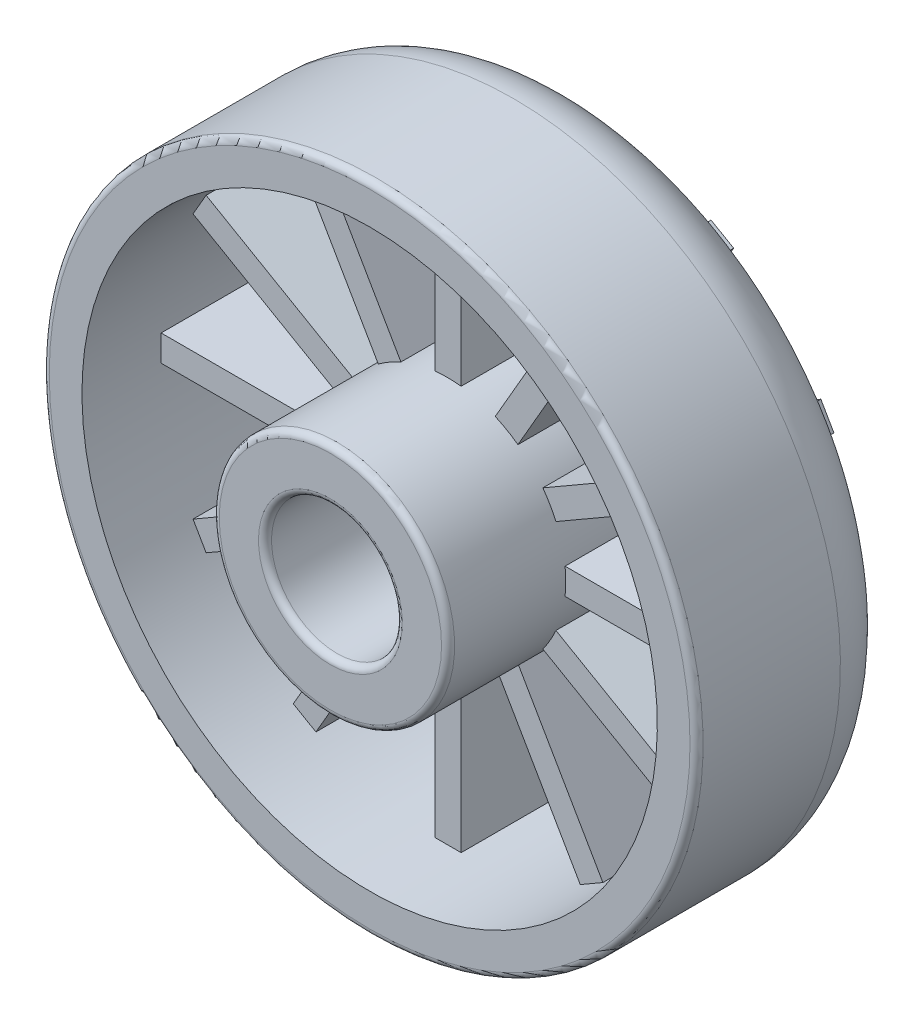
SolidWorks part; units mm, degrees
material "Polyurethane Foam Flexible"
ref_plane "Front Plane" through (0, 0, 0) normal (0, 0, 1) x (1, 0, 0)
ref_plane "Top Plane" through (0, 0, 0) normal (0, 1, 0) x (1, 0, 0)
ref_plane "Right Plane" through (0, 0, 0) normal (1, 0, 0) x (0, 0, -1)
sketch "Sketch1" plane through (0, 0, 0) normal (1, 0, 0) x (0, 0, -1)
  line L0 (-8, 0) -> (8, 0)
  line L1 (-8, 0) -> (-8, -3)
  line L2 (8, 0) -> (8, -25)
  line L3 (8, -25) -> (-11, -25)
  line L4 (-11, -25) -> (-11, -16)
  line L5 (5, -16) -> (5, -3)
  line L6 (5, -16) -> (-11, -16)
  line L7 (5, -3) -> (-8, -3)
  point P4 (0, 0)
  dimension "D1" = 16
  dimension "D2" = 25
  dimension "D3" = 3
  dimension "D4" = 9
  dimension "D5" = 3
  dimension "D6" = 19
revolve "Revolve1" add sketch "Sketch1" angle 360 about L3
fillet "Fillet1" radius 5 1 edges at (0, 0, -8)
ref_plane "Plane1" through (0, 0, -8) normal (0, 0, -1) x (-1, 0, 0)
sketch "Sketch2" plane through (0, 0, -8) normal (0, 0, -1) x (-1, 0, 0)
  line L0 (-1, -3.0557) -> (1, -3.0557)
  line L1 (1, -16.0557) -> (1, -3.0557)
  line L2 (-1, -16.0557) -> (-1, -3.0557)
  line L3 (0, -3.0557) -> (0, -16) construction
  arc A2 (1, -16.0557) -> (-1, -16.0557) centre (0, -25) ccw
  point P3 (1, -25)
  point P4 (0, 0)
  point P6 (1, 0)
  point P7 (-1, -25)
  point P8 (-1, 0)
  dimension "D1" = 13
  dimension "D3" = 2
  dimension "D4" = 9
  dimension "D2" = 13
  dimension "D5" = 8.9443
extrude "Boss-Extrude1" add sketch "Sketch2" against normal blind 10
pattern_circular "CirPattern1" count 12 over 360 about axis through (0, -25, 0) along (0, 0, 1) of "Boss-Extrude1"
ref_plane "Plane2" through (0, 0, 11) normal (0, 0, 1) x (1, 0, 0)
sketch "Sketch3" plane through (0, 0, 11) normal (0, 0, 1) x (1, 0, 0)
  circle A0 centre (0, -25) radius 5
  dimension "D1" = 10
extrude "Cut-Extrude1" cut sketch "Sketch3" against normal blind 14
fillet "Fillet2" radius 0.5 2 edges at (5, -25, 11) (0, -16, 11)
fillet "Fillet3" radius 0.5 1 edges at (0, 0, 8)
